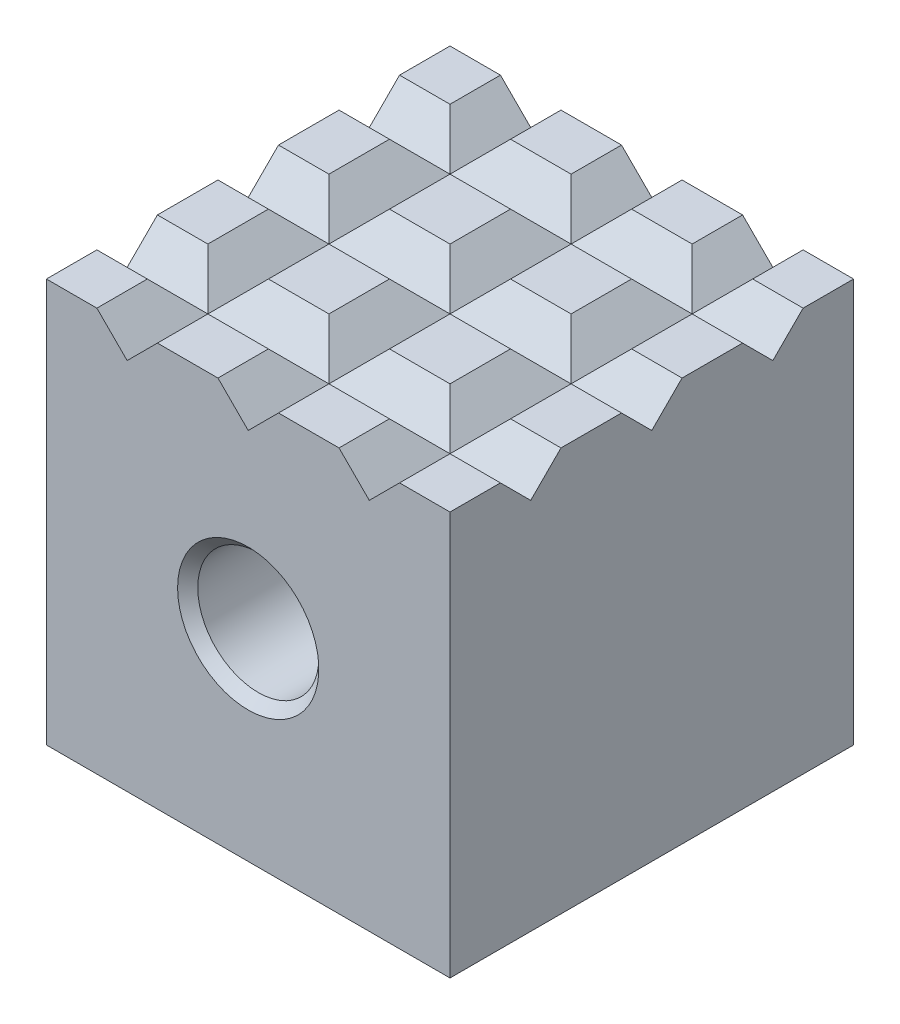
SolidWorks part; units mm, degrees
ref_plane "Front Plane" through (0, 0, 0) normal (0, 0, 1) x (1, 0, 0)
ref_plane "Top Plane" through (0, 0, 0) normal (0, 1, 0) x (1, 0, 0)
ref_plane "Right Plane" through (0, 0, 0) normal (1, 0, 0) x (0, 0, -1)
sketch "Sketch1" plane through (0, 0, 0) normal (0, 1, 0) x (1, 0, 0)
  line L1 (10, -10) -> (-10, -10)
  line L2 (10, -10) -> (10, 10)
  line L3 (10, 10) -> (-10, 10)
  line L4 (-10, -10) -> (-10, 10)
  line L5 (10, -10) -> (-10, 10) construction
  line L6 (10, 10) -> (-10, -10) construction
  point P0 (0, 0)
  dimension "D1" = 20
extrude "Boss-Extrude1" add sketch "Sketch1" along normal blind 20
sketch "Sketch2" plane through (0, 0, 10) normal (0, 0, 1) x (1, 0, 0)
  line L0 (-10, 0) -> (10, 20) construction
  circle A0 centre (0, 10) radius 3
  dimension "D1" = 6
extrude "Cut-Extrude1" cut sketch "Sketch2" against normal through all
chamfer "Chamfer1" distance 0.5 angle 45 2 edges at (3, 10, 10) (3, 10, -10)
sketch "Sketch3" plane through (0, 0, 0) normal (0, 0, 1) x (1, 0, 0)
  line L0 (0, 20) -> (0, 0) construction
  line L1 (-10, 20) -> (10, 20) construction
  line L2 (-10, 18.5) -> (10, 18.5) construction
  line L3 (-10, 20) -> (-10, 0) construction
  line L4 (10, 20) -> (10, 0) construction
  line L5 (0, 18.5) -> (-2.5, 21)
  line L6 (-2.5, 21) -> (2.5, 21)
  line L7 (2.5, 21) -> (0, 18.5)
  line L8 (3.5, 21) -> (8.5, 21)
  line L9 (6, 18.5) -> (3.5, 21)
  line L10 (8.5, 21) -> (6, 18.5)
  line L11 (-2.5, 21) -> (2.5, 21)
  line L12 (0, 18.5) -> (-2.5, 21)
  line L13 (2.5, 21) -> (0, 18.5)
  line L14 (-8.5, 21) -> (-3.5, 21)
  line L15 (-6, 18.5) -> (-8.5, 21)
  line L16 (-3.5, 21) -> (-6, 18.5)
  dimension "D1" = 1.5
  dimension "D2" = 90
  dimension "D3" = 45
  dimension "D4" = 2.5
  dimension "D5" = 2
  dimension "D6" = 2
extrude "Cut-Extrude2" cut sketch "Sketch3" against normal through all both and the other way through all contours L16 L14 L15 | L7 L6 L5 | L10 L8 L9
sketch "Sketch4" plane through (0, 0, 0) normal (1, 0, 0) x (0, 0, -1)
  line L0 (0, 20) -> (0, 0) construction
  line L1 (-10.206, 18.5) -> (10.206, 18.5) construction
  line L2 (0, 18.5) -> (-2.5, 21)
  line L3 (-2.5, 21) -> (2.5, 21)
  line L4 (2.5, 21) -> (0, 18.5)
  line L5 (3.5, 21) -> (8.5, 21)
  line L6 (6, 18.5) -> (3.5, 21)
  line L7 (8.5, 21) -> (6, 18.5)
  line L8 (-2.5, 21) -> (2.5, 21)
  line L9 (0, 18.5) -> (-2.5, 21)
  line L10 (2.5, 21) -> (0, 18.5)
  line L11 (-8.5, 21) -> (-3.5, 21)
  line L12 (-6, 18.5) -> (-8.5, 21)
  line L13 (-3.5, 21) -> (-6, 18.5)
  line L14 (-10, 20) -> (10, 20) construction
  point P22 (0, 20)
  dimension "D1" = 1.5
  dimension "D2" = 6
  dimension "D3" = 6
  dimension "D4" = 5
  dimension "D5" = 5
  dimension "D6" = 5
  dimension "D7" = 45
  dimension "D8" = 90
  dimension "D9" = 1
  dimension "D10" = 1
  dimension "D11" = 1
  dimension "D12" = 1
  dimension "D13" = 3.5355
  dimension "D14" = 3.5355
extrude "Cut-Extrude3" cut sketch "Sketch4" against normal through all both and the other way through all contours L13 L11 L12 | L4 L3 L2 | L7 L5 L6
